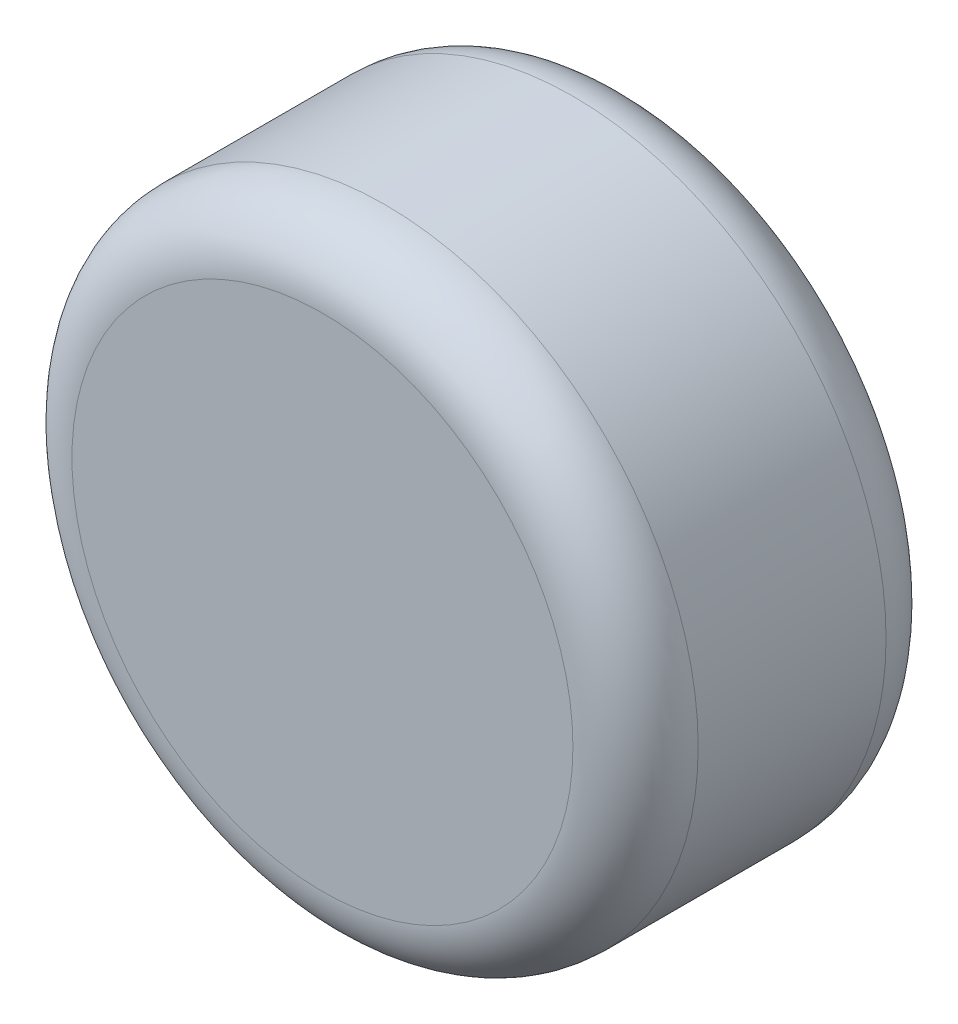
SolidWorks part; units mm, degrees
ref_plane "正面" through (0, 0, 0) normal (0, 0, 1) x (1, 0, 0)
ref_plane "平面" through (0, 0, 0) normal (0, 1, 0) x (1, 0, 0)
ref_plane "右側面" through (0, 0, 0) normal (1, 0, 0) x (0, 0, -1)
sketch "ｽｹｯﾁ2" plane through (0, 0, 0) normal (0, 0, 1) x (1, 0, 0)
  circle A0 centre (0, 0) radius 50
  dimension "D1" = 100
extrude "ﾎﾞｽ - 押し出し2" add sketch "ｽｹｯﾁ2" along normal blind 50
fillet "ﾌｨﾚｯﾄ1" radius 10 2 edges at (50, 0, 50) (50, 0, 0)
